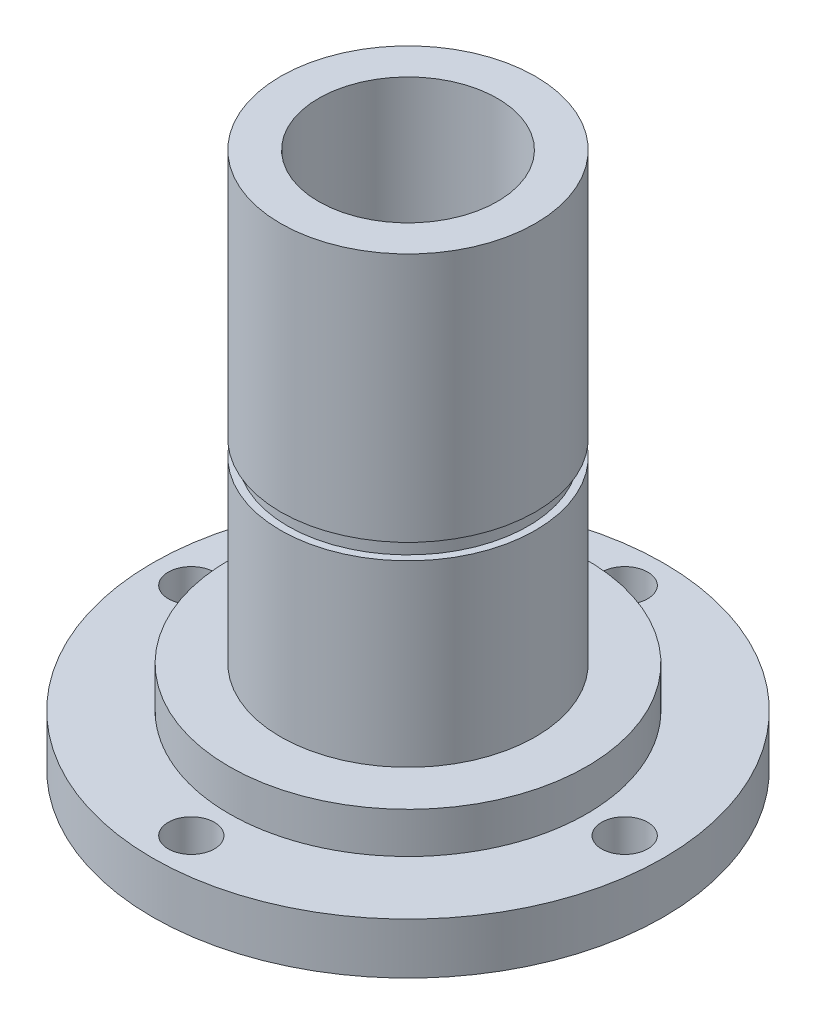
SolidWorks part; units mm, degrees
ref_plane "Front Plane" through (0, 0, 0) normal (0, 0, 1) x (1, 0, 0)
ref_plane "Top Plane" through (0, 0, 0) normal (0, 1, 0) x (1, 0, 0)
ref_plane "Right Plane" through (0, 0, 0) normal (1, 0, 0) x (0, 0, -1)
sketch "Sketch1" plane through (0, 0, 0) normal (0, 1, 0) x (1, 0, 0)
  circle A0 centre (0, 0) radius 11.1125
  circle A1 centre (0, 0) radius 5.5562
  dimension "D1" = 22.225
  dimension "D2" = 11.1125
extrude "Boss-Extrude1" add sketch "Sketch1" along normal blind 5.715
sketch "Sketch2" plane through (0, 5.715, 0) normal (0, 1, 0) x (1, 0, 0)
  circle A0 centre (0, 0) radius 5.5562
  circle A1 centre (0, 0) radius 7.9185
  dimension "D1" = 15.8369
extrude "Boss-Extrude2" add sketch "Sketch2" along normal blind 27.6225
ref_plane "Plane1" through (0, 16.8275, 0) normal (0, 1, 0) x (-1, 0, 0)
sketch "Sketch3" plane through (0, 16.8275, 0) normal (0, 1, 0) x (-1, 0, 0)
  circle A0 centre (0, 0) radius 7.4676
  dimension "D1" = 14.9352
extrude "Cut-Extrude1" cut sketch "Sketch3" along normal blind 0.9906 flip side to cut
sketch "Sketch4" plane through (0, 0, 0) normal (0, -1, 0) x (1, 0, 0)
  circle A0 centre (0, 13.462) radius 1.4351
  circle A1 centre (13.462, 0) radius 1.4351
  circle A2 centre (0, -13.462) radius 1.4351
  circle A3 centre (-13.462, 0) radius 1.4351
  circle A4 centre (0, 0) radius 11.1125
  circle A5 centre (0, 0) radius 15.875
  dimension "D1" = 2.8702
  dimension "D4" = 31.75
  dimension "D2" = 13.462
  dimension "D3" = 4
extrude "Boss-Extrude3" add sketch "Sketch4" against normal blind 3.175 separate body
cosmetic thread "Cosmetic Thread1" parameters "D2"=3.5052
cosmetic thread "Cosmetic Thread2" parameters "D2"=3.5052
cosmetic thread "Cosmetic Thread3" parameters "D2"=3.5052
cosmetic thread "Cosmetic Thread4" parameters "D2"=3.5052
